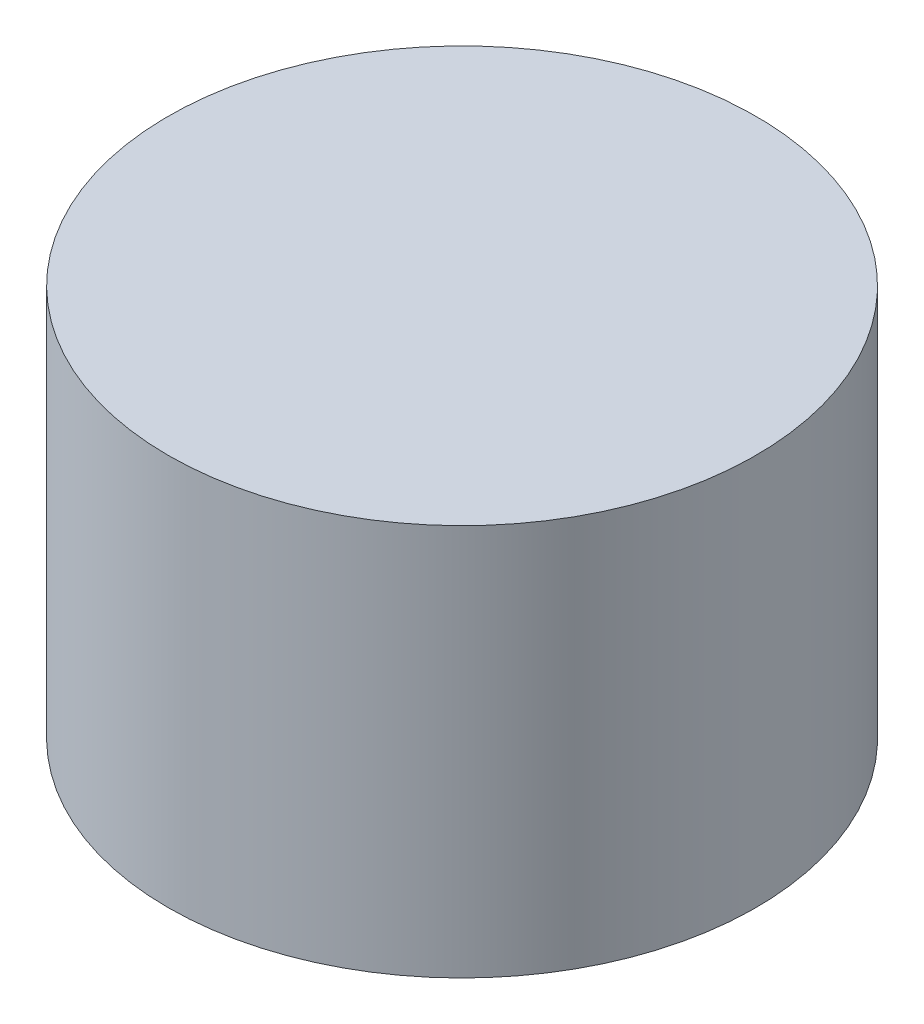
SolidWorks part; units mm, degrees
ref_plane "前视基准面" through (0, 0, 0) normal (0, 0, 1) x (1, 0, 0)
ref_plane "上视基准面" through (0, 0, 0) normal (0, 1, 0) x (1, 0, 0)
ref_plane "右视基准面" through (0, 0, 0) normal (1, 0, 0) x (0, 0, -1)
sketch "草图1" plane through (0, 0, 0) normal (0, 1, 0) x (1, 0, 0)
  circle A0 centre (0, 0) radius 1.5
  dimension "D1" = 3
extrude "凸台-拉伸1" add sketch "草图1" along normal blind 2
